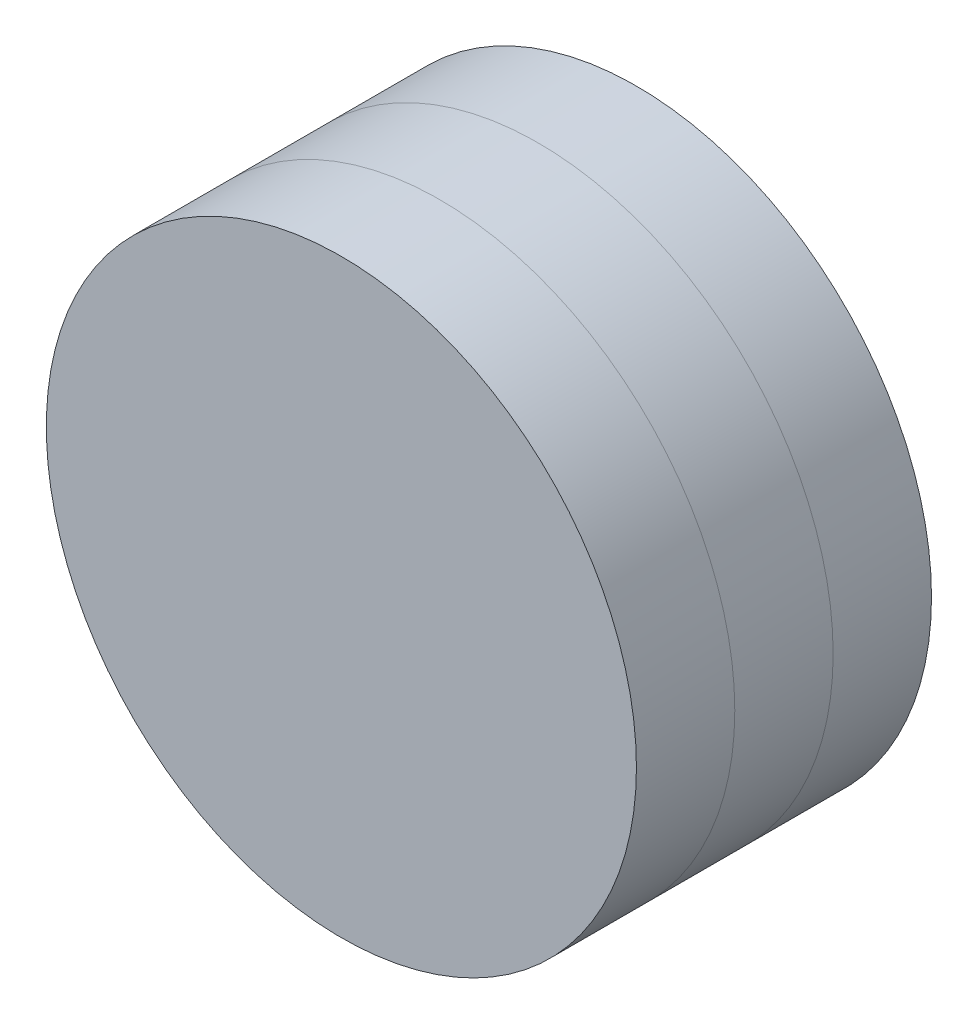
SolidWorks part; units mm, degrees
ref_plane "Front Plane" through (0, 0, 0) normal (0, 0, 1) x (1, 0, 0)
ref_plane "Top Plane" through (0, 0, 0) normal (0, 1, 0) x (1, 0, 0)
ref_plane "Right Plane" through (0, 0, 0) normal (1, 0, 0) x (0, 0, -1)
sketch "Sketch1" plane through (0, 0, 0) normal (0, 0, 1) x (1, 0, 0)
  circle A0 centre (0, 0) radius 60
  dimension "D1" = 120
extrude "Boss-Extrude1" add sketch "Sketch1" along normal blind 20
sketch "Sketch2" plane through (0, 0, 20) normal (0, 0, 1) x (1, 0, 0)
  circle A1 centre (0, 0) radius 60
  circle A2 centre (0, 0) radius 60
  dimension "D1" = 0
extrude "Boss-Extrude2" add sketch "Sketch2" along normal blind 20 separate body
sketch "Sketch3" plane through (0, 0, 40) normal (0, 0, 1) x (1, 0, 0)
  circle A1 centre (0, 0) radius 60
  circle A2 centre (0, 0) radius 60
  dimension "D1" = 0
extrude "Boss-Extrude3" add sketch "Sketch3" along normal blind 20 separate body
